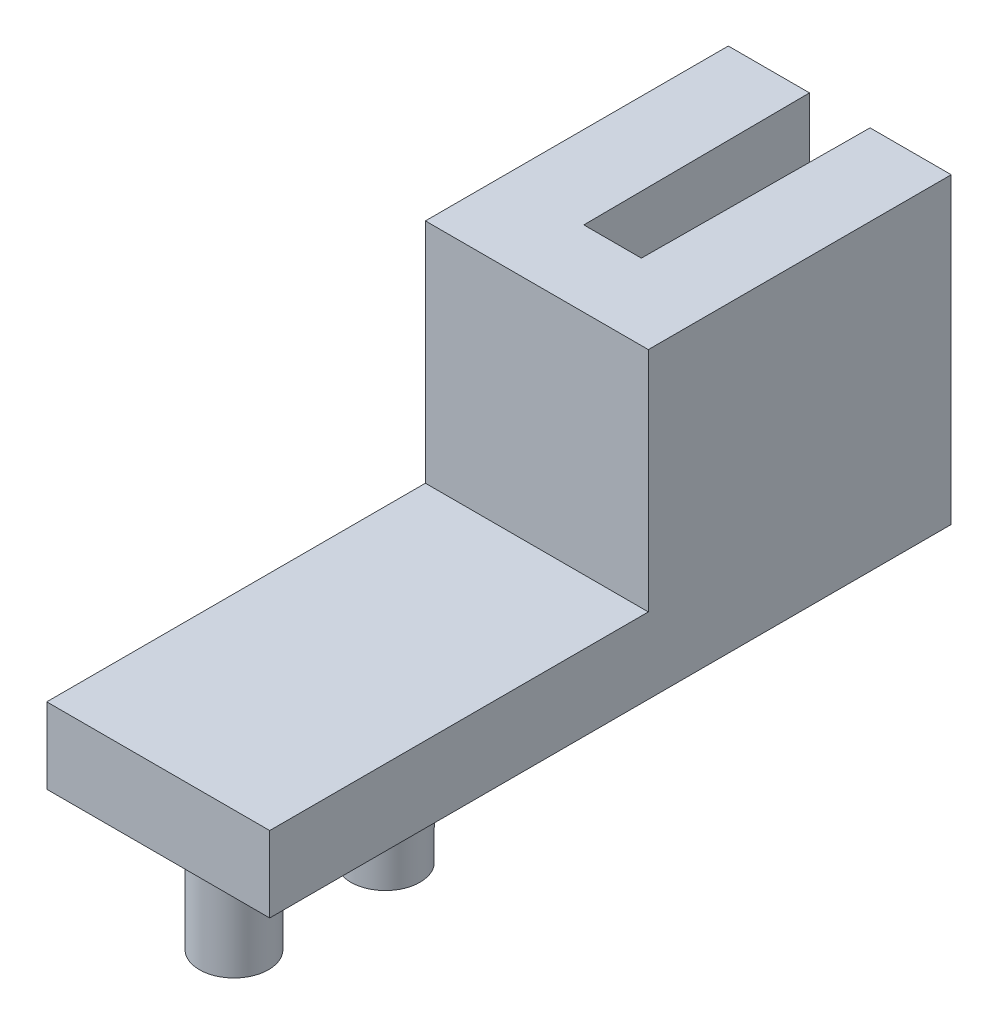
SolidWorks part; units mm, degrees
ref_plane "Front Plane" through (0, 0, 0) normal (0, 0, 1) x (1, 0, 0)
ref_plane "Top Plane" through (0, 0, 0) normal (0, 1, 0) x (1, 0, 0)
ref_plane "Right Plane" through (0, 0, 0) normal (1, 0, 0) x (0, 0, -1)
sketch "Sketch2" plane through (0, 0, 0) normal (1, 0, 0) x (0, 0, -1)
  line L0 (3.175, 9.525) -> (3.175, -3.175) construction
  line L1 (-15.875, 0) -> (0, 0)
  line L2 (-15.875, 0) -> (-15.875, -3.175)
  line L3 (-15.875, -3.175) -> (0, -3.175)
  line L4 (0, 0) -> (0, -3.175)
  line L5 (0, -3.175) -> (12.7, -3.175)
  line L6 (0, -3.175) -> (0, 9.525)
  line L7 (0, 9.525) -> (12.7, 9.525)
  line L8 (12.7, -3.175) -> (12.7, 9.525)
  line L9 (-6.35, 0) -> (-6.35, -3.175) construction
  line L10 (-12.7, 0) -> (-12.7, -3.175) construction
  dimension "D1" = 12.7
  dimension "D2" = 3.175
  dimension "D3" = 3.175
  dimension "D4" = 9.525
  dimension "D5" = 6.35
  dimension "D6" = 12.7
  dimension "D7" = 3.175
extrude "Boss-Extrude1" add sketch "Sketch2" along normal blind 9.3472 contours L4 L1 L2 L3 | L5 L8 L7 L6 L4
sketch "Sketch3" plane through (0, 9.525, 0) normal (0, 1, 0) x (1, 0, 0)
  line L0 (9.3472, 12.7) -> (0, 12.7) construction
  line L1 (3.4671, 12.7) -> (5.8801, 12.7)
  line L2 (3.4671, 12.7) -> (3.4671, 3.175)
  line L3 (3.4671, 3.175) -> (5.8801, 3.175)
  line L4 (5.8801, 12.7) -> (5.8801, 3.175)
  line L5 (9.3472, 0) -> (0, 0) construction
  line L6 (9.3472, 0) -> (0, 0) construction
  line L7 (3.4671, 3.175) -> (3.4036, 12.7)
  line L8 (5.8801, 3.175) -> (5.9436, 12.7)
  line L9 (5.9436, 12.7) -> (3.4036, 12.7)
  point P6 (4.6736, 3.175)
  point P9 (4.6736, 0)
  dimension "D1" = 2.413
  dimension "D2" = 3.175
  dimension "D4" = 2.54
extrude "Cut-Extrude1" cut sketch "Sketch3" against normal through all
sketch "Sketch4" plane through (0, -3.175, 0) normal (0, -1, 0) x (1, 0, 0)
  line L0 (3.4671, -3.175) -> (5.8801, -3.175) construction
  circle A0 centre (4.6736, 12.7) radius 1.45
  circle A2 centre (4.6736, 6.35) radius 1.45
  point P7 (4.6736, -3.175)
  dimension "D1" = 2.9
extrude "Boss-Extrude2" add sketch "Sketch4" along normal blind 5.08
